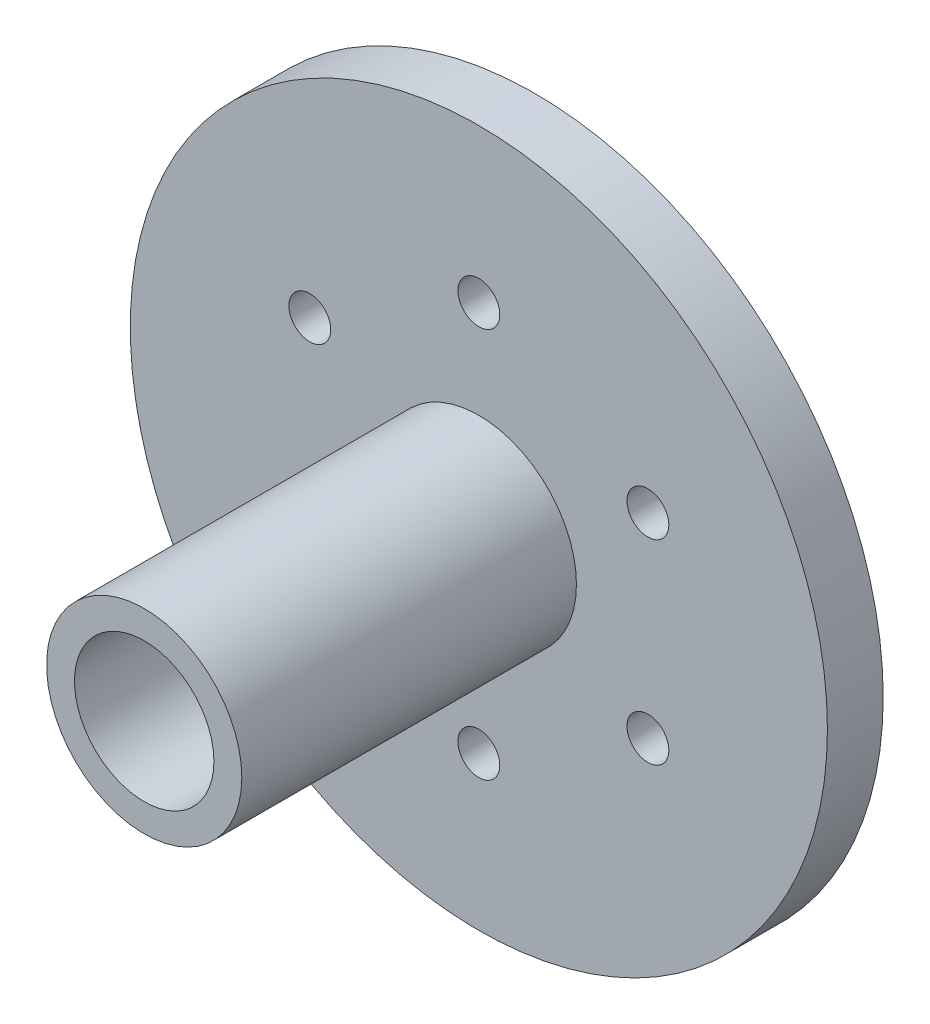
SolidWorks part; units mm, degrees
ref_plane "Front Plane" through (0, 0, 0) normal (0, 0, 1) x (1, 0, 0)
ref_plane "Top Plane" through (0, 0, 0) normal (0, 1, 0) x (1, 0, 0)
ref_plane "Right Plane" through (0, 0, 0) normal (1, 0, 0) x (0, 0, -1)
sketch "Sketch1" plane through (0, 0, 0) normal (0, 0, 1) x (1, 0, 0)
  circle A0 centre (0, 0) radius 25
  dimension "D1" = 50
extrude "Boss-Extrude1" add sketch "Sketch1" along normal blind 4
sketch "Sketch2" plane through (0, 0, 4) normal (0, 0, 1) x (1, 0, 0)
  circle A0 centre (0, 0) radius 7
  circle A1 centre (0, 0) radius 5
  dimension "D1" = 14
  dimension "D2" = 10
extrude "Boss-Extrude2" add sketch "Sketch2" along normal blind 24
sketch "Sketch3" plane through (0, 0, 0) normal (0, 0, -1) x (-1, 0, 0)
  line L0 (0, 0) -> (0, 14) construction
  circle A0 centre (0, 14) radius 1.5
  circle A1 centre (12.1244, 7) radius 1.5
  circle A2 centre (12.1244, -7) radius 1.5
  circle A3 centre (0, -14) radius 1.5
  circle A4 centre (-12.1244, -7) radius 1.5
  circle A5 centre (-12.1244, 7) radius 1.5
  dimension "D1" = 3
  dimension "D2" = 14
  dimension "D4" = 14
  dimension "D3" = 6
extrude "Cut-Extrude1" cut sketch "Sketch3" against normal blind 24
sketch "Sketch4" plane through (0, 0, 0) normal (0, 0, -1) x (-1, 0, 0)
  point P0 (0, 14)
